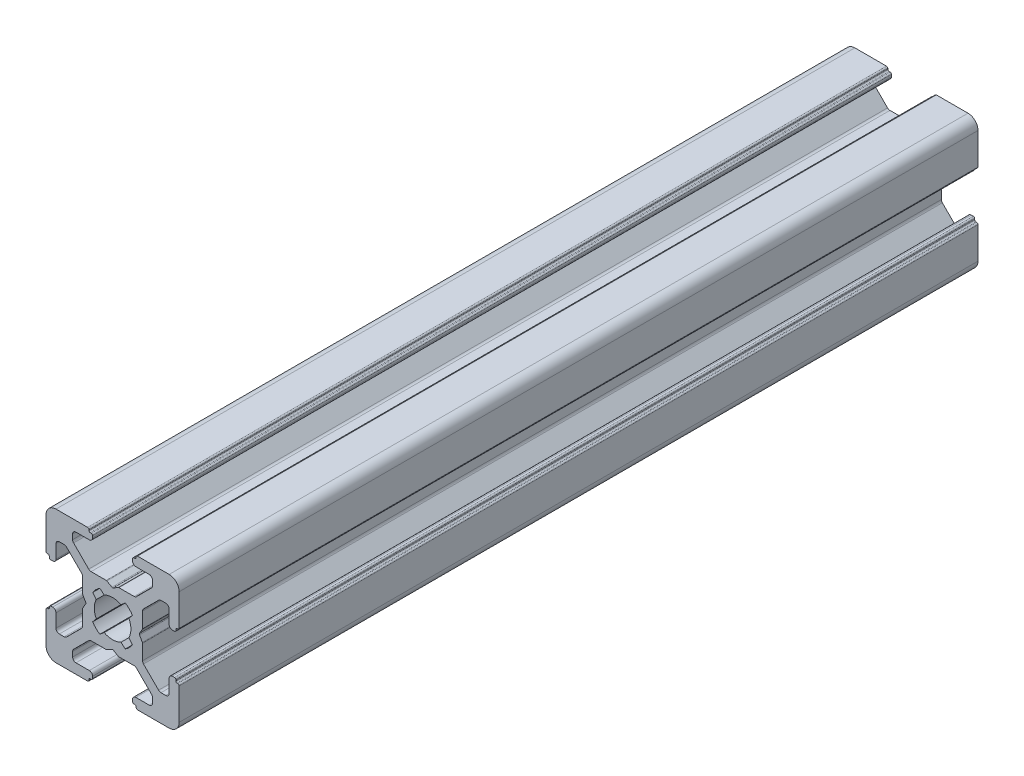
SolidWorks part; units mm, degrees
ref_plane "Front Plane" through (0, 0, 0) normal (0, 0, 1) x (1, 0, 0)
ref_plane "Top Plane" through (0, 0, 0) normal (0, 1, 0) x (1, 0, 0)
ref_plane "Right Plane" through (0, 0, 0) normal (1, 0, 0) x (0, 0, -1)
sketch "Sketch1" plane through (0, 0, 0) normal (0, 0, 1) x (1, 0, 0)
  line L0 (0, 13.3675) -> (0, -10.9159) construction
  line L1 (-12.9725, 0) -> (15.1887, 0) construction
  line L2 (-3.5, 8.5) -> (-5.5, 8.5)
  line L3 (-3.55, 9.7) -> (-3.55, 9.8)
  line L4 (-6, 7.2678) -> (-6, 8)
  line L5 (-7.2678, 6) -> (-8, 6)
  line L6 (-3.75, 10) -> (-8.5, 10)
  line L7 (-9.7, 3.55) -> (-9.8, 3.55)
  line L8 (-9.5, 3.2) -> (-9.5, 3.35)
  line L9 (-9, 3) -> (-9.3, 3)
  line L10 (-4.4732, 0.8536) -> (-4.0381, 0.1)
  line L11 (-4.5, 3.2322) -> (-4.5, 0.9536)
  line L12 (-8.5, 3.5) -> (-8.5, 5.5)
  line L13 (-10, 3.75) -> (-10, 8.5)
  line L14 (-3.5858, 4.6464) -> (-5.8536, 6.9142)
  line L15 (-4.6464, 3.5858) -> (-6.9142, 5.8536)
  line L16 (-3.2, 9.5) -> (-3.35, 9.5)
  line L17 (-3, 9) -> (-3, 9.3)
  line L18 (-0.8536, 4.4732) -> (-0.1, 4.0381)
  line L19 (-3.2322, 4.5) -> (-0.9536, 4.5)
  line L20 (-1.2582, 2.4453) -> (-1.9139, 2.9896)
  line L21 (-2.4453, 1.2582) -> (-2.9922, 1.9099)
  line L22 (3.5, -8.5) -> (5.5, -8.5)
  line L23 (3.55, -9.7) -> (3.55, -9.8)
  line L24 (6, -7.2678) -> (6, -8)
  line L25 (7.2678, -6) -> (8, -6)
  line L26 (3.75, -10) -> (8.5, -10)
  line L27 (9.7, -3.55) -> (9.8, -3.55)
  line L28 (9.5, -3.2) -> (9.5, -3.35)
  line L29 (9, -3) -> (9.3, -3)
  line L30 (4.4732, -0.8536) -> (4.0381, -0.1)
  line L31 (4.5, -3.2322) -> (4.5, -0.9536)
  line L32 (8.5, -3.5) -> (8.5, -5.5)
  line L33 (10, -3.75) -> (10, -8.5)
  line L34 (3.5858, -4.6464) -> (5.8536, -6.9142)
  line L35 (4.6464, -3.5858) -> (6.9142, -5.8536)
  line L36 (3.2, -9.5) -> (3.35, -9.5)
  line L37 (3, -9) -> (3, -9.3)
  line L38 (0.8536, -4.4732) -> (0.1, -4.0381)
  line L39 (3.2322, -4.5) -> (0.9536, -4.5)
  line L40 (1.2582, -2.4453) -> (1.9139, -2.9896)
  line L41 (2.4453, -1.2582) -> (2.9922, -1.9099)
  line L42 (-2.4453, -1.2582) -> (-2.9922, -1.9099)
  line L43 (-1.2582, -2.4453) -> (-1.9139, -2.9896)
  line L44 (-3.2322, -4.5) -> (-0.9536, -4.5)
  line L45 (-0.8536, -4.4732) -> (-0.1, -4.0381)
  line L46 (-3, -9) -> (-3, -9.3)
  line L47 (-3.2, -9.5) -> (-3.35, -9.5)
  line L48 (-4.6464, -3.5858) -> (-6.9142, -5.8536)
  line L49 (-3.5858, -4.6464) -> (-5.8536, -6.9142)
  line L50 (-10, -3.75) -> (-10, -8.5)
  line L51 (-8.5, -3.5) -> (-8.5, -5.5)
  line L52 (-4.5, -3.2322) -> (-4.5, -0.9536)
  line L53 (-4.4732, -0.8536) -> (-4.0381, -0.1)
  line L54 (-9, -3) -> (-9.3, -3)
  line L55 (-9.5, -3.2) -> (-9.5, -3.35)
  line L56 (-9.7, -3.55) -> (-9.8, -3.55)
  line L57 (2.4453, 1.2582) -> (2.9922, 1.9099)
  line L58 (1.2582, 2.4453) -> (1.9139, 2.9896)
  line L59 (3.2322, 4.5) -> (0.9536, 4.5)
  line L60 (0.8536, 4.4732) -> (0.1, 4.0381)
  line L61 (-3.75, -10) -> (-8.5, -10)
  line L62 (-7.2678, -6) -> (-8, -6)
  line L63 (-6, -7.2678) -> (-6, -8)
  line L64 (3, 9) -> (3, 9.3)
  line L65 (3.2, 9.5) -> (3.35, 9.5)
  line L66 (4.6464, 3.5858) -> (6.9142, 5.8536)
  line L67 (3.5858, 4.6464) -> (5.8536, 6.9142)
  line L68 (10, 3.75) -> (10, 8.5)
  line L69 (8.5, 3.5) -> (8.5, 5.5)
  line L70 (4.5, 3.2322) -> (4.5, 0.9536)
  line L71 (4.4732, 0.8536) -> (4.0381, 0.1)
  line L72 (9, 3) -> (9.3, 3)
  line L73 (9.5, 3.2) -> (9.5, 3.35)
  line L74 (9.7, 3.55) -> (9.8, 3.55)
  line L75 (3.75, 10) -> (8.5, 10)
  line L76 (7.2678, 6) -> (8, 6)
  line L77 (6, 7.2678) -> (6, 8)
  line L78 (3.55, 9.7) -> (3.55, 9.8)
  line L79 (3.5, 8.5) -> (5.5, 8.5)
  line L80 (-3.55, -9.7) -> (-3.55, -9.8)
  line L81 (-3.5, -8.5) -> (-5.5, -8.5)
  arc A0 (-10, 8.5) -> (-8.5, 10) centre (-8.5, 8.5) cw
  arc A1 (-8.5, 5.5) -> (-8, 6) centre (-8, 5.5) cw
  arc A2 (-7.2678, 6) -> (-6.9142, 5.8536) centre (-7.2678, 5.5) cw
  arc A3 (-5.8536, 6.9142) -> (-6, 7.2678) centre (-5.5, 7.2678) cw
  arc A4 (-6, 8) -> (-5.5, 8.5) centre (-5.5, 8) cw
  arc A5 (-9.7, 3.55) -> (-9.5, 3.35) centre (-9.7, 3.35) cw
  arc A6 (-9.8, 3.55) -> (-10, 3.75) centre (-9.8, 3.75) cw
  arc A7 (-9.3, 3) -> (-9.5, 3.2) centre (-9.3, 3.2) cw
  arc A8 (-8.5, 3.5) -> (-9, 3) centre (-9, 3.5) cw
  arc A9 (-4.6464, 3.5858) -> (-4.5, 3.2322) centre (-5, 3.2322) cw
  arc A10 (-4.4732, 0.8536) -> (-4.5, 0.9536) centre (-4.3, 0.9536) cw
  arc A11 (-4.0381, 0.1) -> (-4.0381, -0.1) centre (-4.2113, 0) cw
  arc A12 (-3.2, 9.5) -> (-3, 9.3) centre (-3.2, 9.3) cw
  arc A13 (-0.9536, 4.5) -> (-0.8536, 4.4732) centre (-0.9536, 4.3) cw
  arc A14 (-2.9922, 1.9099) -> (-1.9139, 2.9896) centre (0, 0) cw
  arc A15 (-3.2322, 4.5) -> (-3.5858, 4.6464) centre (-3.2322, 5) cw
  arc A16 (-3.75, 10) -> (-3.55, 9.8) centre (-3.75, 9.8) cw
  arc A17 (-3.35, 9.5) -> (-3.55, 9.7) centre (-3.35, 9.7) cw
  arc A18 (2.4453, -1.2582) -> (2.4453, 1.2582) centre (0, 0) ccw
  arc A19 (-3, 9) -> (-3.5, 8.5) centre (-3.5, 9) cw
  arc A20 (-2.4453, -1.2582) -> (-2.4453, 1.2582) centre (0, 0) cw
  arc A21 (10, -8.5) -> (8.5, -10) centre (8.5, -8.5) cw
  arc A22 (8.5, -5.5) -> (8, -6) centre (8, -5.5) cw
  arc A23 (7.2678, -6) -> (6.9142, -5.8536) centre (7.2678, -5.5) cw
  arc A24 (5.8536, -6.9142) -> (6, -7.2678) centre (5.5, -7.2678) cw
  arc A25 (6, -8) -> (5.5, -8.5) centre (5.5, -8) cw
  arc A26 (9.7, -3.55) -> (9.5, -3.35) centre (9.7, -3.35) cw
  arc A27 (9.8, -3.55) -> (10, -3.75) centre (9.8, -3.75) cw
  arc A28 (9.3, -3) -> (9.5, -3.2) centre (9.3, -3.2) cw
  arc A29 (8.5, -3.5) -> (9, -3) centre (9, -3.5) cw
  arc A30 (4.6464, -3.5858) -> (4.5, -3.2322) centre (5, -3.2322) cw
  arc A31 (4.4732, -0.8536) -> (4.5, -0.9536) centre (4.3, -0.9536) cw
  arc A32 (3.2, -9.5) -> (3, -9.3) centre (3.2, -9.3) cw
  arc A33 (-0.1, -4.0381) -> (0.1, -4.0381) centre (0, -4.2113) cw
  arc A34 (0.9536, -4.5) -> (0.8536, -4.4732) centre (0.9536, -4.3) cw
  arc A35 (2.9922, -1.9099) -> (1.9139, -2.9896) centre (0, 0) cw
  arc A36 (1.2582, -2.4453) -> (-1.2582, -2.4453) centre (0, 0) cw
  arc A37 (3.2322, -4.5) -> (3.5858, -4.6464) centre (3.2322, -5) cw
  arc A38 (3.75, -10) -> (3.55, -9.8) centre (3.75, -9.8) cw
  arc A39 (3.35, -9.5) -> (3.55, -9.7) centre (3.35, -9.7) cw
  arc A40 (3, -9) -> (3.5, -8.5) centre (3.5, -9) cw
  arc A41 (-3, -9) -> (-3.5, -8.5) centre (-3.5, -9) ccw
  arc A42 (-3.35, -9.5) -> (-3.55, -9.7) centre (-3.35, -9.7) ccw
  arc A43 (-3.75, -10) -> (-3.55, -9.8) centre (-3.75, -9.8) ccw
  arc A44 (-3.2322, -4.5) -> (-3.5858, -4.6464) centre (-3.2322, -5) ccw
  arc A45 (-2.9922, -1.9099) -> (-1.9139, -2.9896) centre (0, 0) ccw
  arc A46 (-0.9536, -4.5) -> (-0.8536, -4.4732) centre (-0.9536, -4.3) ccw
  arc A47 (-3.2, -9.5) -> (-3, -9.3) centre (-3.2, -9.3) ccw
  arc A48 (-4.4732, -0.8536) -> (-4.5, -0.9536) centre (-4.3, -0.9536) ccw
  arc A49 (3, 9) -> (3.5, 8.5) centre (3.5, 9) ccw
  arc A50 (3.35, 9.5) -> (3.55, 9.7) centre (3.35, 9.7) ccw
  arc A51 (3.75, 10) -> (3.55, 9.8) centre (3.75, 9.8) ccw
  arc A52 (3.2322, 4.5) -> (3.5858, 4.6464) centre (3.2322, 5) ccw
  arc A53 (1.2582, 2.4453) -> (-1.2582, 2.4453) centre (0, 0) ccw
  arc A54 (-4.6464, -3.5858) -> (-4.5, -3.2322) centre (-5, -3.2322) ccw
  arc A55 (-8.5, -3.5) -> (-9, -3) centre (-9, -3.5) ccw
  arc A56 (-9.3, -3) -> (-9.5, -3.2) centre (-9.3, -3.2) ccw
  arc A57 (-9.8, -3.55) -> (-10, -3.75) centre (-9.8, -3.75) ccw
  arc A58 (-9.7, -3.55) -> (-9.5, -3.35) centre (-9.7, -3.35) ccw
  arc A59 (-6, -8) -> (-5.5, -8.5) centre (-5.5, -8) ccw
  arc A60 (2.9922, 1.9099) -> (1.9139, 2.9896) centre (0, 0) ccw
  arc A61 (0.9536, 4.5) -> (0.8536, 4.4732) centre (0.9536, 4.3) ccw
  arc A62 (-0.1, 4.0381) -> (0.1, 4.0381) centre (0, 4.2113) ccw
  arc A63 (-5.8536, -6.9142) -> (-6, -7.2678) centre (-5.5, -7.2678) ccw
  arc A64 (-7.2678, -6) -> (-6.9142, -5.8536) centre (-7.2678, -5.5) ccw
  arc A65 (-8.5, -5.5) -> (-8, -6) centre (-8, -5.5) ccw
  arc A66 (-10, -8.5) -> (-8.5, -10) centre (-8.5, -8.5) ccw
  arc A67 (3.2, 9.5) -> (3, 9.3) centre (3.2, 9.3) ccw
  arc A68 (4.0381, 0.1) -> (4.0381, -0.1) centre (4.2113, 0) ccw
  arc A69 (4.4732, 0.8536) -> (4.5, 0.9536) centre (4.3, 0.9536) ccw
  arc A70 (4.6464, 3.5858) -> (4.5, 3.2322) centre (5, 3.2322) ccw
  arc A71 (8.5, 3.5) -> (9, 3) centre (9, 3.5) ccw
  arc A72 (9.3, 3) -> (9.5, 3.2) centre (9.3, 3.2) ccw
  arc A73 (9.8, 3.55) -> (10, 3.75) centre (9.8, 3.75) ccw
  arc A74 (9.7, 3.55) -> (9.5, 3.35) centre (9.7, 3.35) ccw
  arc A75 (6, 8) -> (5.5, 8.5) centre (5.5, 8) ccw
  arc A76 (5.8536, 6.9142) -> (6, 7.2678) centre (5.5, 7.2678) ccw
  arc A77 (7.2678, 6) -> (6.9142, 5.8536) centre (7.2678, 5.5) ccw
  arc A78 (8.5, 5.5) -> (8, 6) centre (8, 5.5) ccw
  arc A79 (10, 8.5) -> (8.5, 10) centre (8.5, 8.5) ccw
  dimension "D4" = 5.5
  dimension "D1" = 6
  dimension "D2" = 20
  dimension "D3" = 20
  dimension "D5" = 5.5
  dimension "D6" = 10
  dimension "D7" = 6
  dimension "D8" = 6
  dimension "D9" = 6
extrude "Extrude1" add sketch "Sketch1" along normal blind 120
